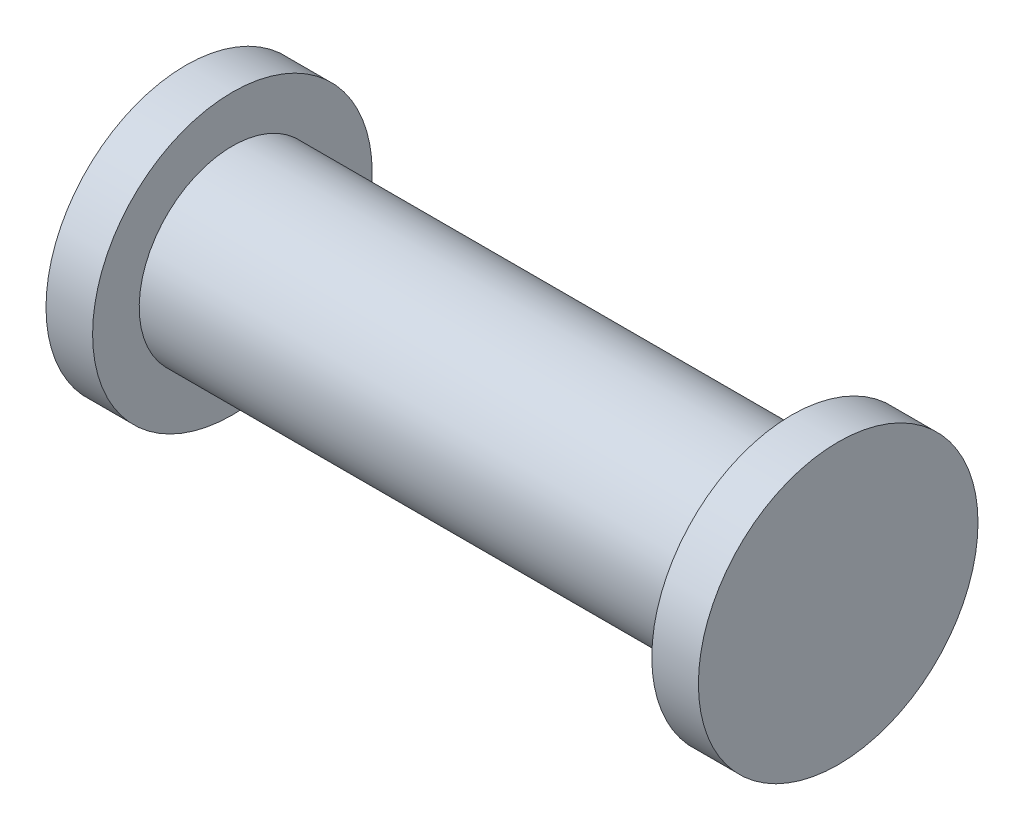
SolidWorks part; units mm, degrees
material "3.1325 (EN-AW 2017A)"
ref_plane "Płaszczyzna przednia" through (0, 0, 0) normal (0, 0, 1) x (1, 0, 0)
ref_plane "Płaszczyzna górna" through (0, 0, 0) normal (0, 1, 0) x (1, 0, 0)
ref_plane "Płaszczyzna prawa" through (0, 0, 0) normal (1, 0, 0) x (0, 0, -1)
sketch "Szkic1" plane through (0, 0, 0) normal (0, 0, 1) x (1, 0, 0)
  line L0 (0, 0) -> (6.5, 0)
  line L1 (0, 0) -> (0, 1.5)
  line L2 (0, 1.5) -> (0.5, 1.5)
  line L3 (0.5, 1.5) -> (0.5, 1)
  line L4 (0.5, 1) -> (6.5, 1)
  line L5 (6.5, 1) -> (6.5, 1.5)
  line L6 (6.5, 0) -> (7, 0) construction
  line L7 (7, 0) -> (7, -1.7727) construction
  line L8 (6.5, 0) -> (7, 0)
  line L9 (6.5, 1.5) -> (7, 1.5)
  line L10 (7, 1.5) -> (7, 0)
  dimension "D1" = 2
  dimension "D2" = 6
  dimension "D3" = 0.5
  dimension "D4" = 7
  dimension "D5" = 3
  dimension "D6" = 0.5
  dimension "D7" = 3
revolve "Obrót1" add sketch "Szkic1" angle 360 about L8
